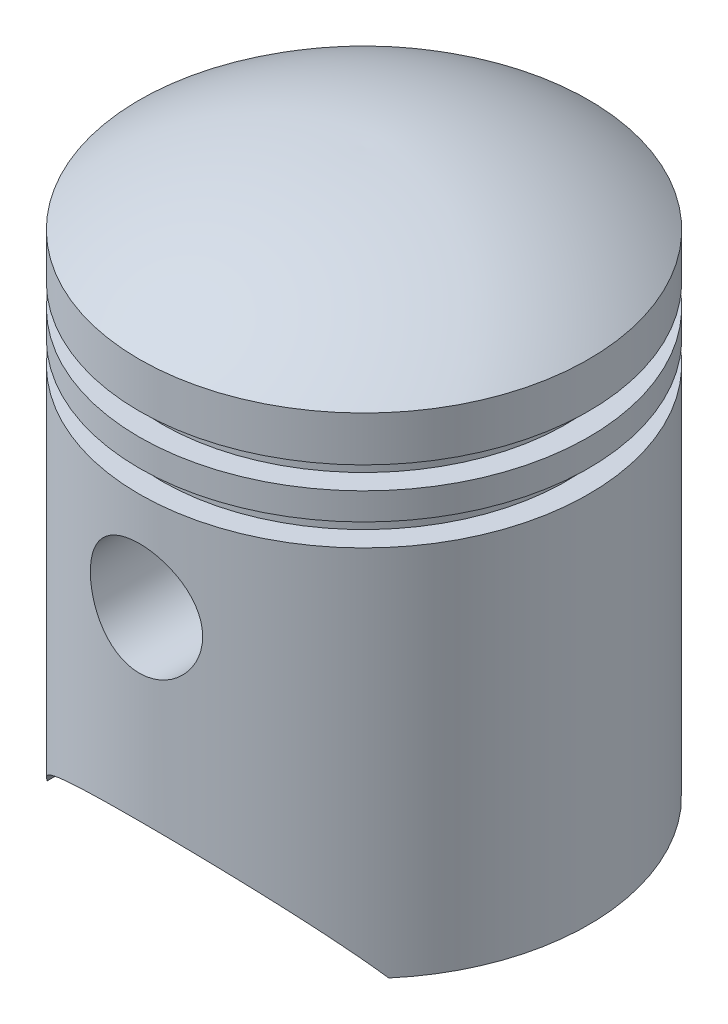
SolidWorks part; units mm, degrees
ref_plane "Front Plane" through (0, 0, 0) normal (0, 0, 1) x (1, 0, 0)
ref_plane "Top Plane" through (0, 0, 0) normal (0, 1, 0) x (1, 0, 0)
ref_plane "Right Plane" through (0, 0, 0) normal (1, 0, 0) x (0, 0, -1)
sketch "Sketch2" plane through (0, 0, 0) normal (0, 0, 1) x (1, 0, 0)
  line L0 (25, 0) -> (25, 41.5)
  line L1 (25, 49.5) -> (22.5, 49.5)
  line L2 (22.5, 49.5) -> (22.5, 47)
  line L3 (22.5, 47) -> (25, 47)
  line L4 (25, 44) -> (22.5, 44)
  line L5 (22.5, 44) -> (22.5, 41.5)
  line L6 (22.5, 41.5) -> (25, 41.5)
  line L7 (25, 49.5) -> (25, 54.5)
  line L8 (25, 44) -> (25, 47)
  line L9 (23, 0) -> (23, 39.5)
  line L10 (20.5, 39.5) -> (23, 39.5)
  line L11 (20.5, 45.5) -> (20.5, 39.5)
  line L12 (20.5, 45.5) -> (20.5, 45.5)
  line L13 (20.5, 45.5) -> (20.5, 45.5)
  line L14 (20.5, 45.5) -> (20.5, 45.5)
  line L15 (20.5, 51.5) -> (20.5, 45.5)
  line L16 (23, 51.5) -> (20.5, 51.5)
  line L17 (23, 51.5) -> (23, 53.4845)
  line L18 (25, 0) -> (23, 0)
  line L20 (0, 62.5) -> (0, 60.4994)
  arc A0 (25, 54.5) -> (0, 62.5) centre (0.9839, 22.5121) ccw
  arc A1 (23, 53.4845) -> (0, 60.4994) centre (0.9839, 22.5121) ccw
  arc A2 (23, 53.4845) -> (0.0492, 60.5006) centre (0.9839, 22.5121) ccw construction
  dimension "D4" = 40
  dimension "D1" = 25
  dimension "D2" = 62.5
  dimension "D3" = 54.5
  dimension "D5" = 5
  dimension "D6" = 2.5
  dimension "D7" = 2.5
  dimension "D8" = 3
  dimension "D9" = 2.5
  dimension "D10" = 2
revolve "Revolve1" add sketch "Sketch2" angle 360 about L20
sketch "Sketch3" plane through (0, 0, 0) normal (0, 0, 1) x (1, 0, 0)
  line L1 (0, 30.5) -> (0, 62.5) construction
  line L2 (-25, 0) -> (25, 0) construction
  line L3 (-19, 0) -> (19, 0)
  circle A0 centre (0, 30.5) radius 6.25
  arc A1 (-19, 0) -> (19, 0) centre (0, -13.05) cw
  point P11 (0, 10)
  dimension "D1" = 12.5
  dimension "D4" = 10
  dimension "D2" = 32
  dimension "D3" = 38
extrude "Cut-Extrude1" cut sketch "Sketch3" against normal through all both and the other way through all
sketch "Sketch4" plane through (0, 0, 0) normal (0, 0, 1) x (1, 0, 0)
  circle A0 centre (0, 30.5) radius 7.25
  circle A1 centre (0, 30.5) radius 6.25
  dimension "D1" = 14.5
  dimension "D2" = 12.5
extrude "Boss-Extrude3" add sketch "Sketch4" along normal up to surface (11.9257 mm away) from offset 12
mirror "Mirror2" about plane through (0, 0, 0) normal (0, 0, 1) of "Boss-Extrude3"
